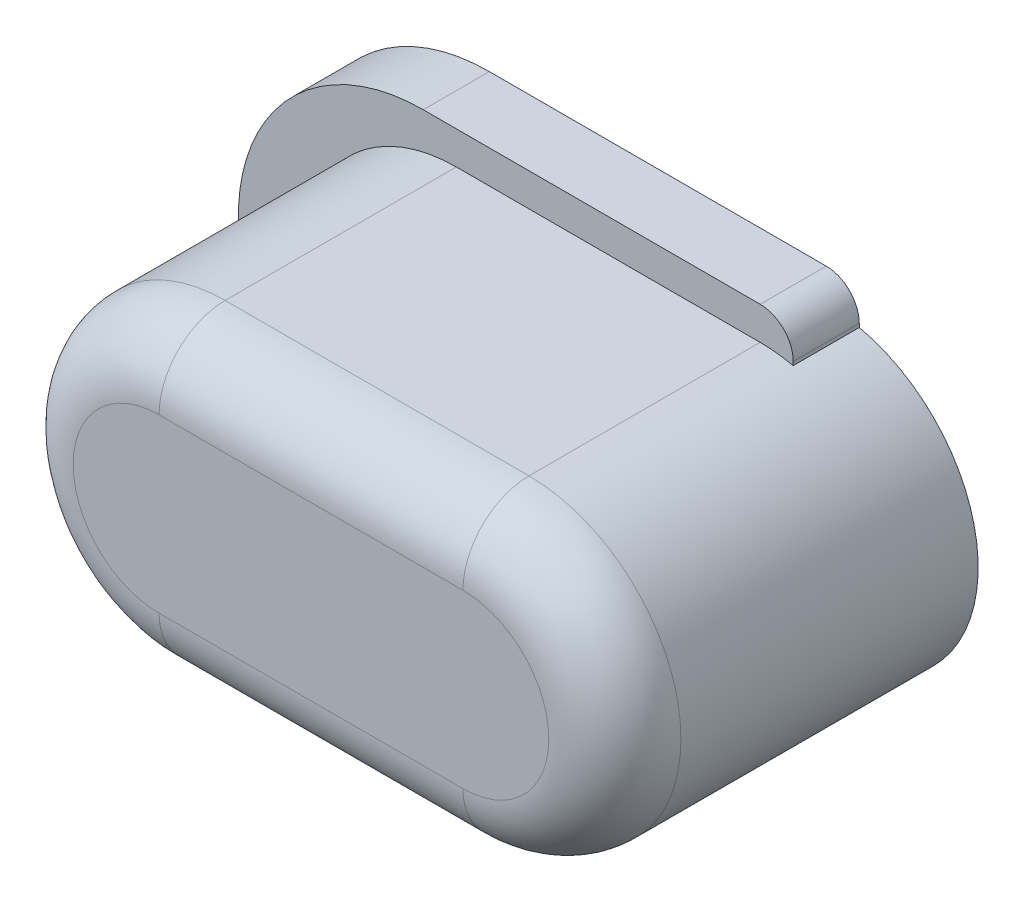
SolidWorks part; units mm, degrees
ref_plane "Front Plane" through (0, 0, 0) normal (0, 0, 1) x (1, 0, 0)
ref_plane "Top Plane" through (0, 0, 0) normal (0, 1, 0) x (1, 0, 0)
ref_plane "Right Plane" through (0, 0, 0) normal (1, 0, 0) x (0, 0, -1)
sketch "草图1" plane through (0, 0, 0) normal (0, 0, 1) x (1, 0, 0)
  line L1 (2.3, -2.3) -> (-2.3, -2.3)
  line L3 (2.3, 2.3) -> (-2.3, 2.3)
  arc A0 (-2.3, 2.3) -> (-2.3, -2.3) centre (-2.3, 0) ccw
  arc A1 (2.3, -2.3) -> (2.3, 2.3) centre (2.3, 0) ccw
  point P0 (0, 0)
  dimension "D3" = 2.3
  dimension "D4" = 2.3
  dimension "D1" = 4.6
  dimension "D2" = 4.6
extrude "凸台-拉伸1" add sketch "草图1" along normal blind 5.5 contours L3 A0 L1 A1
sketch "草图2" plane through (0, 0, 0) normal (0, 0, -1) x (-1, 0, 0)
  line L0 (0, 0) -> (-7.4405, 0) construction
  line L1 (2.8, -2.8) -> (-2.3, -2.8)
  line L3 (2.8, 2.8) -> (-2.3, 2.8)
  line L4 (-2.8, 2.3) -> (-2.8, -2.3)
  arc A1 (2.8, -2.8) -> (2.8, 2.8) centre (2.8, 0) ccw
  arc A2 (-2.3, -2.8) -> (-2.8, -2.3) centre (-2.3, -2.3) cw
  arc A3 (-2.3, 2.8) -> (-2.8, 2.3) centre (-2.3, 2.3) ccw
  point P0 (0, 0)
  point P11 (-2.8, -2.8)
  point P14 (-2.8, 2.8)
  dimension "D3" = 0.5
  dimension "D1" = 5.6
  dimension "D2" = 5.6
extrude "凸台-拉伸2" add sketch "草图2" against normal blind 1 contours L1 A2 L4 A3 L3 A1
sketch "草图3" plane through (0, 0, 0) normal (0, 0, -1) x (-1, 0, 0)
  circle A0 centre (0, 0) radius 2
  dimension "D1" = 4
extrude "切除-拉伸1" cut sketch "草图3" against normal blind 0.5
fillet "圆角1" radius 1 4 edges at (4.6, 0, 5.5) (0, -2.3, 5.5) (-4.6, 0, 5.5) (0, 2.3, 5.5)
